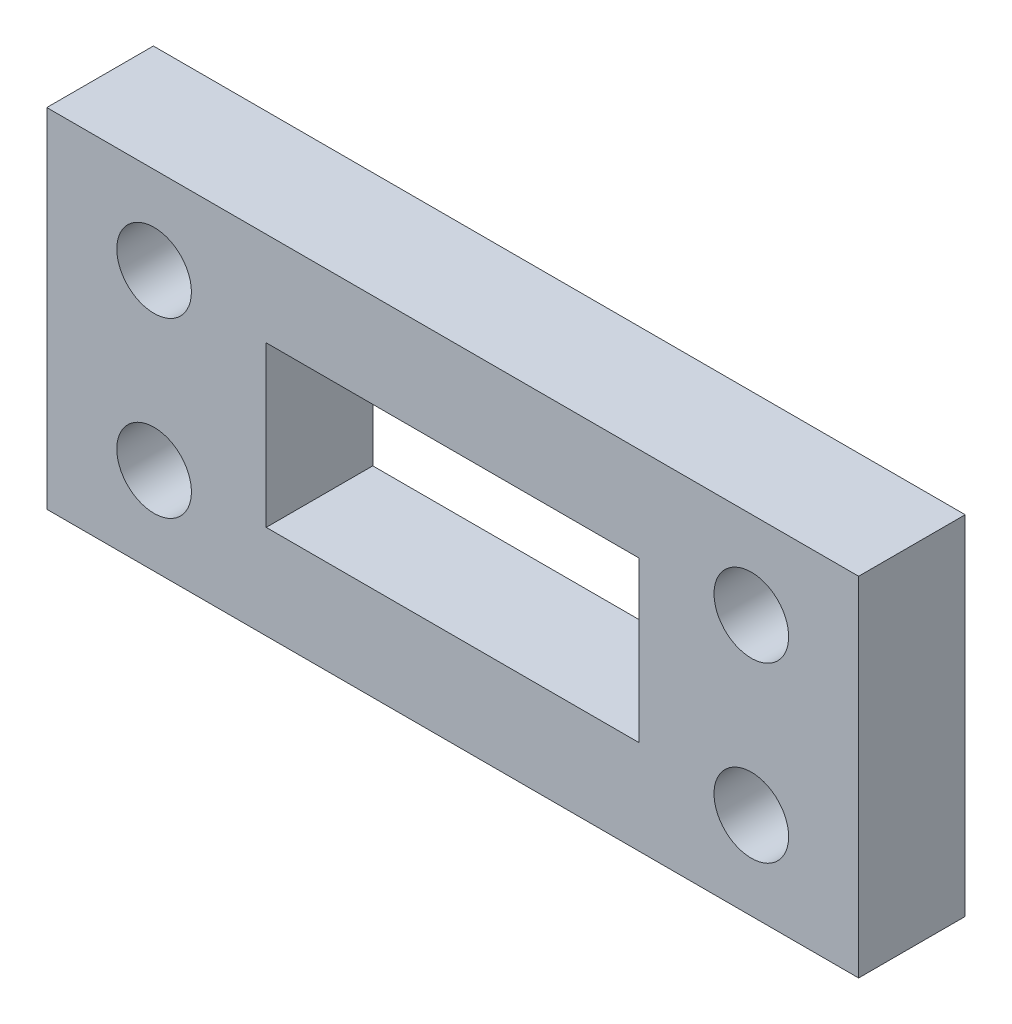
SolidWorks part; units mm, degrees
material "AISI 304"
ref_plane "Alzado" through (0, 0, 0) normal (0, 0, 1) x (1, 0, 0)
ref_plane "Planta" through (0, 0, 0) normal (0, 1, 0) x (1, 0, 0)
ref_plane "Vista lateral" through (0, 0, 0) normal (1, 0, 0) x (0, 0, -1)
sketch "Croquis1" plane through (0, 0, 0) normal (0, 0, 1) x (1, 0, 0)
  line L0 (0, 32.6465) -> (0, -32.6465) construction
  line L1 (76.1751, 32.6465) -> (-76.1751, 32.6465)
  line L2 (76.1751, 32.6465) -> (76.1751, -32.6465)
  line L3 (76.1751, -32.6465) -> (-76.1751, -32.6465)
  line L4 (-76.1751, 32.6465) -> (-76.1751, -32.6465)
  line L5 (76.1751, 32.6465) -> (-76.1751, -32.6465) construction
  line L6 (76.1751, -32.6465) -> (-76.1751, 32.6465) construction
  line L7 (-76.1751, 0) -> (76.1751, 0) construction
  line L9 (-35, 15) -> (35, 15)
  line L10 (-35, 15) -> (-35, -15)
  line L11 (-35, -15) -> (35, -15)
  line L12 (35, 15) -> (35, -15)
  line L13 (-35, 15) -> (35, -15) construction
  line L14 (-35, -15) -> (35, 15) construction
  circle A0 centre (-56.039, 16.2505) radius 7
  circle A1 centre (56.039, 16.2505) radius 7
  circle A2 centre (56.039, -16.2505) radius 7
  circle A3 centre (-56.039, -16.2505) radius 7
  point P0 (0, 0)
  point P18 (0, 0)
extrude "Saliente-Extruir1" add sketch "Croquis1" along normal blind 20
